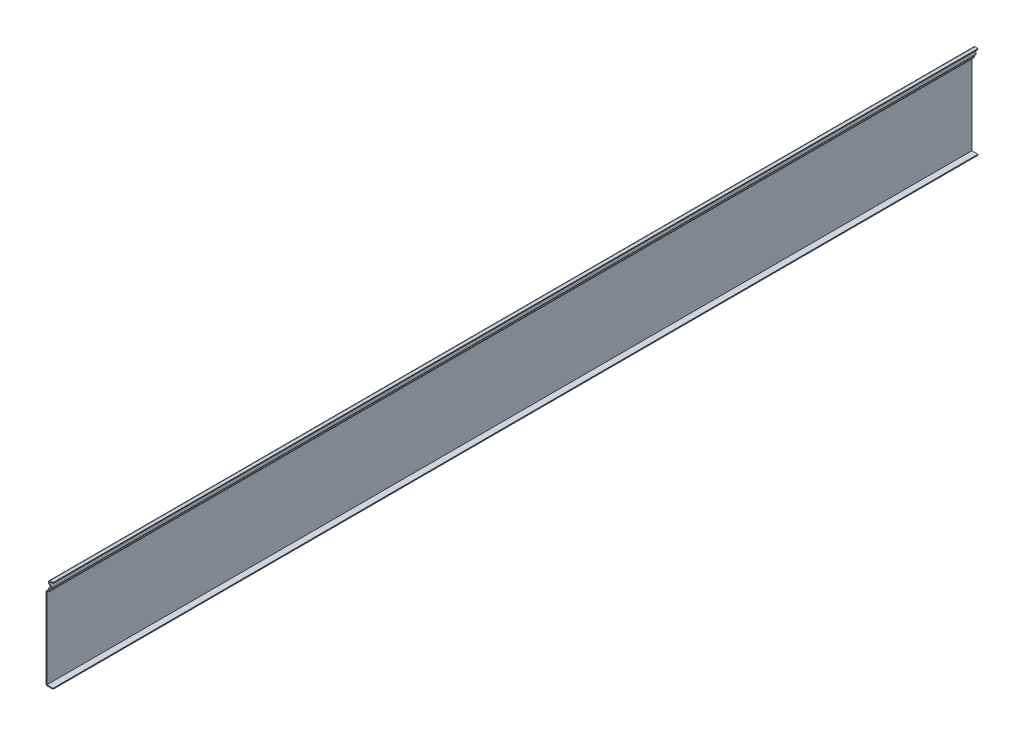
SolidWorks part; units mm, degrees
ref_plane "Front Plane" through (0, 0, 0) normal (0, 0, 1) x (1, 0, 0)
ref_plane "Top Plane" through (0, 0, 0) normal (0, 1, 0) x (1, 0, 0)
ref_plane "Right Plane" through (0, 0, 0) normal (1, 0, 0) x (0, 0, -1)
sketch "Sketch1" plane through (0, 0, 0) normal (0, 0, 1) x (1, 0, 0)
  line L0 (0, 0) -> (-9.525, 0)
  line L1 (-9.525, 0) -> (-9.525, 109.5375)
  line L2 (-6.35, 112.7125) -> (-6.35, 115.8875)
  line L3 (-3.7978, 125.4125) -> (0, 125.4125)
  arc A0 (-9.525, 109.5375) -> (-6.35, 112.7125) centre (-6.35, 109.5375) cw
  arc A2 (-6.35, 115.8875) -> (-5.0739, 120.65) centre (-6.35, 118.4397) ccw
  arc A3 (-5.0739, 120.65) -> (-3.7978, 125.4125) centre (-3.7978, 122.8603) cw
  point P11 (-5.0384, 108.3592)
  point P12 (0, 0)
  point P14 (0, 0)
  dimension "D6" = 6.35
  dimension "D1" = 125.4125
  dimension "D2" = 9.525
  dimension "D3" = 112.7125
  dimension "D4" = 3.175
  dimension "D5" = 3.175
extrude "Extrude-Thin1" add sketch "Sketch1" against normal blind 1254.125 thin
fillet "Fillet1" radius 1.27 3 edges at (-9.525, 0, -627.0625) (-5.08, 110.9574, -627.0625) (-6.35, 115.8875, -627.0625)
